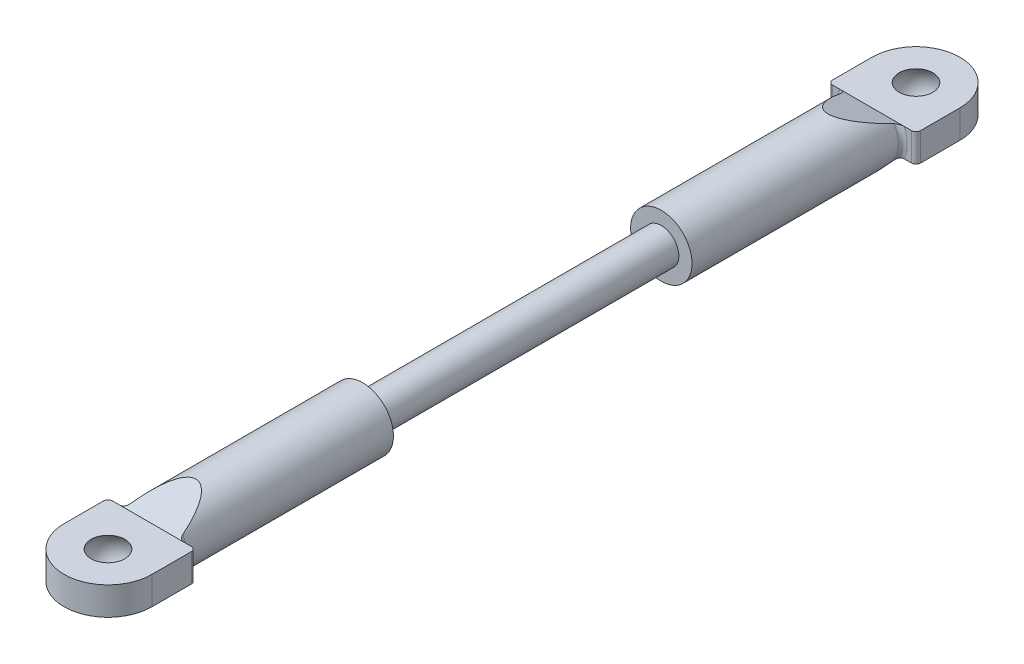
SolidWorks part; units mm, degrees
ref_plane "Front Plane" through (0, 0, 0) normal (0, 0, 1) x (1, 0, 0)
ref_plane "Top Plane" through (0, 0, 0) normal (0, 1, 0) x (1, 0, 0)
ref_plane "Right Plane" through (0, 0, 0) normal (1, 0, 0) x (0, 0, -1)
sketch "Sketch1" plane through (0, 0, 0) normal (0, 0, 1) x (1, 0, 0)
  circle A0 centre (0, 0) radius 2
  dimension "D1" = 4
extrude "Screw Section" add sketch "Sketch1" along normal blind 17 contours A0
sketch "Sketch2" plane through (0, 0, 17) normal (0, 0, 1) x (1, 0, 0)
  circle A0 centre (0, 0) radius 3.5
  dimension "D1" = 7
extrude "Bar Section" add sketch "Sketch2" along normal blind 24
sketch "Sketch3" plane through (0, 0, 0) normal (0, 1, 0) x (1, 0, 0)
  line L0 (5, -41) -> (-5, -41)
  line L1 (-5, -41) -> (-5, -46)
  line L2 (5, -41) -> (5, -46)
  line L3 (-3.5, -41) -> (3.5, -41) construction
  arc A0 (-5, -46) -> (5, -46) centre (0, -46) ccw
  point P4 (0, -51)
  dimension "D1" = 5
  dimension "D2" = 10
  dimension "D3" = 10
extrude "Mount Section" add sketch "Sketch3" along normal mid plane 3.2
sketch "Sketch4" plane through (0, 0, 0) normal (1, 0, 0) x (0, 0, -1)
  line L0 (-36, -3.5) -> (-41, -1.6)
  line L1 (-41, -3.5) -> (-17, -3.5) construction
  line L2 (-41, -1.6) -> (-41, -3.5)
  line L3 (-41, -1.6) -> (-41, -3.5) construction
  line L4 (-41, -3.5) -> (-36, -3.5)
  line L5 (-36, 3.5) -> (-41, 1.6)
  line L6 (-41, 3.5) -> (-41, 1.6) construction
  line L7 (-41, 3.5) -> (-36, 3.5)
  line L9 (-41, 1.6) -> (-41, 3.5)
  dimension "D1" = 5
  dimension "D2" = 1.9
extrude "Bar Taper" cut sketch "Sketch4" against normal through all both and the other way through all
fillet "Mount Fillet" radius 0.5 4 edges at (-5, 0, 41) (3.5, 0, 41) (-3.5, 0, 41) (5, 0, 41)
sketch "Sketch6" plane through (0, 0, 0) normal (1, 0, 0) x (0, 0, -1)
  line L0 (-46, 1.6) -> (-46, -1.6) construction
  line L1 (-51, -1.6) -> (-46, -1.6) construction
  line L2 (-46, 1.6) -> (-51, 1.6) construction
  line L4 (-47.9209, -1.6) -> (-46, -1.6)
  line L5 (-46, -1.6) -> (-46, 1.6)
  line L6 (-46, 1.6) -> (-47.9209, 1.6)
  arc A0 (-47.9209, -1.6) -> (-47.9209, 1.6) centre (-46, 0) cw
  dimension "D1" = 2.5
revolve "Ball Hole" cut sketch "Sketch6" angle 360 about L5
mirror "Mirror" of "Ball Hole", "Bar Section", "Bar Taper", "Mount Section", "Mount Fillet", "Screw Section"
ref_point "Point1"
ref_point "Point2"
